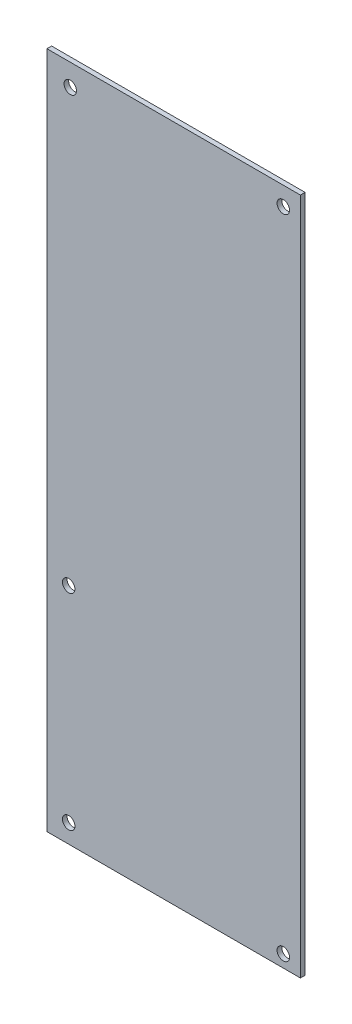
SolidWorks part; units mm, degrees
ref_plane "Plan de face" through (0, 0, 0) normal (0, 0, 1) x (1, 0, 0)
ref_plane "Plan de dessus" through (0, 0, 0) normal (0, 1, 0) x (1, 0, 0)
ref_plane "Plan de droite" through (0, 0, 0) normal (1, 0, 0) x (0, 0, -1)
sketch "Main-Sketch" plane through (0, 0, 0) normal (0, 0, 1) x (1, 0, 0)
  line L1 (0, 0) -> (81.5, 0)
  line L2 (0, 0) -> (0, 218)
  line L3 (0, 218) -> (81.5, 218)
  line L4 (81.5, 0) -> (81.5, 218)
  dimension "D1" = 81.5
  dimension "D2" = 218
extrude "Main" add sketch "Main-Sketch" along normal blind 1.5
sketch "Hole-Sketch" plane through (0, 0, 1.5) normal (0, 0, 1) x (1, 0, 0)
  line L0 (0, 0) -> (81.5, 0) construction
  line L1 (81.5, 0) -> (81.5, 218) construction
  line L2 (81.5, 218) -> (0, 218) construction
  line L3 (0, 218) -> (0, 0) construction
  circle A0 centre (7.5, 211) radius 2
  circle A1 centre (76, 212) radius 2
  circle A2 centre (7, 6) radius 2
  circle A3 centre (76, 4) radius 2
  circle A4 centre (7, 72) radius 2
  dimension "D1" = 4
  dimension "D3" = 4
  dimension "D4" = 4
  dimension "D2" = 4
  dimension "D5" = 5.5
  dimension "D6" = 6
  dimension "D7" = 7
  dimension "D8" = 7.5
  dimension "D9" = 7
  dimension "D10" = 6
  dimension "D11" = 5.5
  dimension "D12" = 72
  dimension "D13" = 68.5
  dimension "D14" = 69
extrude "Hole" cut sketch "Hole-Sketch" against normal through all
